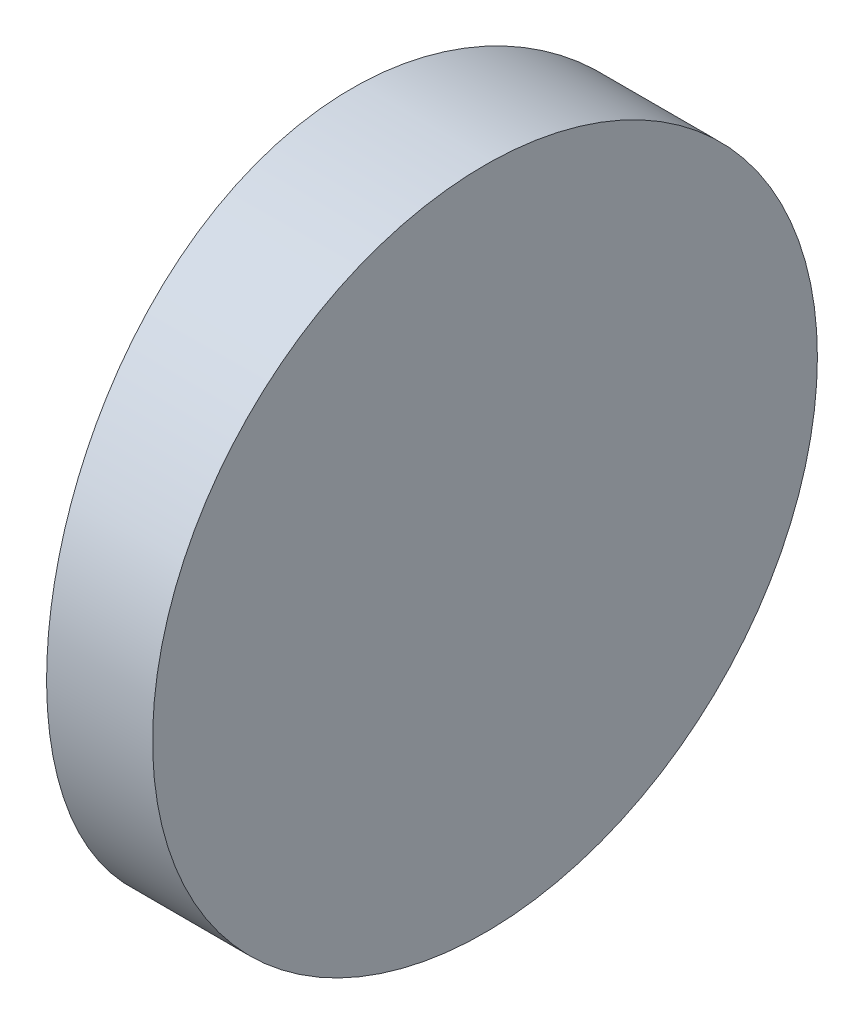
SolidWorks part; units mm, degrees
ref_plane "前视基准面" through (0, 0, 0) normal (0, 0, 1) x (1, 0, 0)
ref_plane "上视基准面" through (0, 0, 0) normal (0, 1, 0) x (1, 0, 0)
ref_plane "右视基准面" through (0, 0, 0) normal (1, 0, 0) x (0, 0, -1)
sketch "草图1" plane through (0, 0, 0) normal (0, 1, 0) x (1, 0, 0)
  line L0 (10.7432, 0) -> (-38.0771, 0) construction
  line L1 (-33.9178, 6.25) -> (-31.9248, 6.25)
  line L2 (-33.9178, -6.25) -> (-31.9248, -6.25)
  line L3 (-31.9248, 6.25) -> (-31.9248, -6.25)
  arc A0 (-33.9178, 6.25) -> (-33.9178, -6.25) centre (4.3552, 0) ccw
  point P2 (-38.0771, 0)
  point P19 (-34.4248, 0)
  point P20 (-31.9248, 0)
  dimension "D2" = 6.25
  dimension "D3" = 38.78
  dimension "D4" = 2.5
  dimension "D1" = 6.25
extrude "凸台-拉伸1" add sketch "草图1" along normal blind 12.5 contours A0 L2 L3 L1
sketch "草图2" plane through (-31.9248, 0, 0) normal (1, 0, 0) x (0, 0, -1)
  line L0 (6.25, 0) -> (-6.25, 0) construction
  line L7 (-6.25, 0) -> (6.25, 0)
  line L8 (6.25, 0) -> (6.25, 12.5)
  line L9 (6.25, 12.5) -> (-6.25, 12.5)
  line L10 (-6.25, 12.5) -> (-6.25, 0)
  line L11 (-6.25, 0) -> (6.25, 0)
  line L12 (6.25, 0) -> (6.25, 12.5)
  line L13 (6.25, 12.5) -> (-6.25, 12.5)
  line L14 (-6.25, 12.5) -> (-6.25, 0)
  circle A0 centre (0, 6.25) radius 6.25
  line M1 (-6.25, 0) -> (6.25, 0)
  line M2 (6.25, 0) -> (6.25, 12.5)
  line M3 (6.25, 12.5) -> (-6.25, 12.5)
  line M4 (-6.25, 12.5) -> (-6.25, 0)
  dimension "D1" = 12.5
  dimension "D2" = 6.25
  dimension "D3" = 0
extrude "切除-拉伸8" cut sketch "草图2" against normal blind 12.7 contours A0 L13 M4 | A0 L12 M3 | A0 L11 M2 | A0 L14 M1
